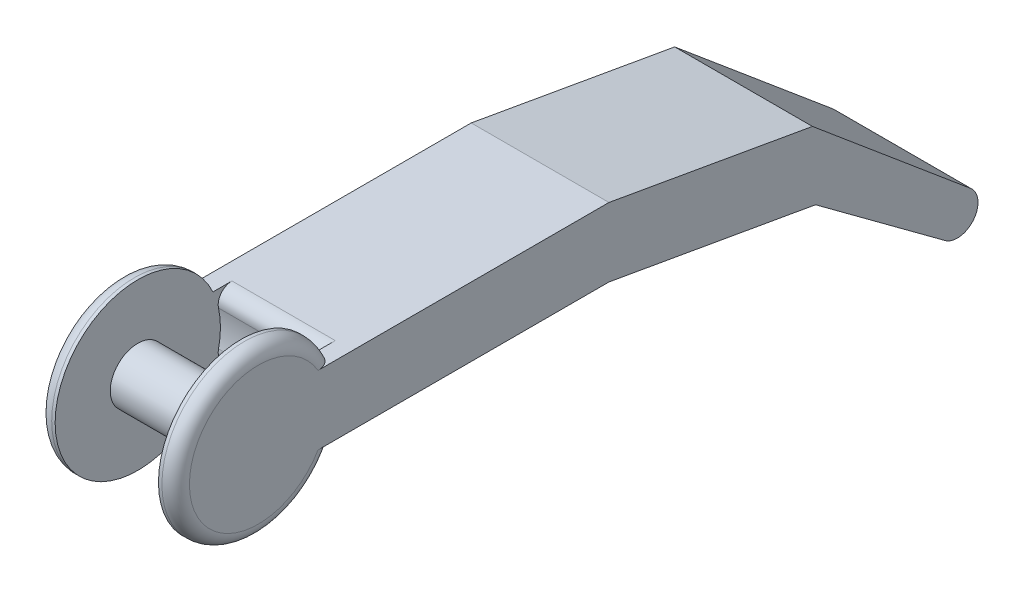
SolidWorks part; units mm, degrees
ref_plane "Front Plane" through (0, 0, 0) normal (0, 0, 1) x (1, 0, 0)
ref_plane "Top Plane" through (0, 0, 0) normal (0, 1, 0) x (1, 0, 0)
ref_plane "Right Plane" through (0, 0, 0) normal (1, 0, 0) x (0, 0, -1)
sketch "Sketch1" plane through (0, 0, 0) normal (1, 0, 0) x (0, 0, -1)
  line L0 (0, 0) -> (-40, 0)
  line L1 (-40, -10) -> (0, -10)
  line L2 (0, -10) -> (0, 0)
  arc A0 (-40, 0) -> (-40, -10) centre (-50.9087, -5) ccw
  dimension "D1" = 12
  dimension "D2" = 5
  dimension "D3" = 10
  dimension "D4" = 40
extrude "Boss-Extrude1" add sketch "Sketch1" along normal blind 20
sketch "Sketch2" plane through (20, 0, 0) normal (1, 0, 0) x (0, 0, -1)
  circle A0 centre (-50.9087, -5) radius 4
  circle A1 centre (-50.9087, -5) radius 12
  dimension "D1" = 8
extrude "Cut-Extrude1" cut sketch "Sketch2" against normal blind 15 from offset 2.5 offset against normal yes
fillet "Fillet1" radius 2 4 edges at (0, -5, 62.9087) (20, -5, 62.9087) (10, -10, 40) (10, 0, 40)
sketch "Sketch3" plane through (20, 0, 0) normal (1, 0, 0) x (0, 0, -1)
  line L0 (0, 0) -> (29.5442, -5.2094)
  line L1 (29.5442, -5.2094) -> (52.5256, -24.4931)
  line L2 (0, 0) -> (-42.2485, 0) construction
  line L3 (0, -10) -> (30, -15.2898)
  line L4 (52.5256, -24.4931) -> (45.7474, -32.571) construction
  line L5 (30, -15.2898) -> (48.6689, -29.0893)
  line L6 (0, 0) -> (0, -10)
  arc A0 (52.5256, -24.4931) -> (48.6689, -29.0893) centre (50.5852, -26.7811) cw
  dimension "D6" = 3
  dimension "D1" = 10
  dimension "D2" = 30
  dimension "D3" = 40
  dimension "D4" = 30
  dimension "D5" = 30
  dimension "D7" = 5.9999
extrude "Boss-Extrude2" add sketch "Sketch3" against normal blind 20
equation "\"D5@Sketch3\"=\"D2@Sketch3\""
